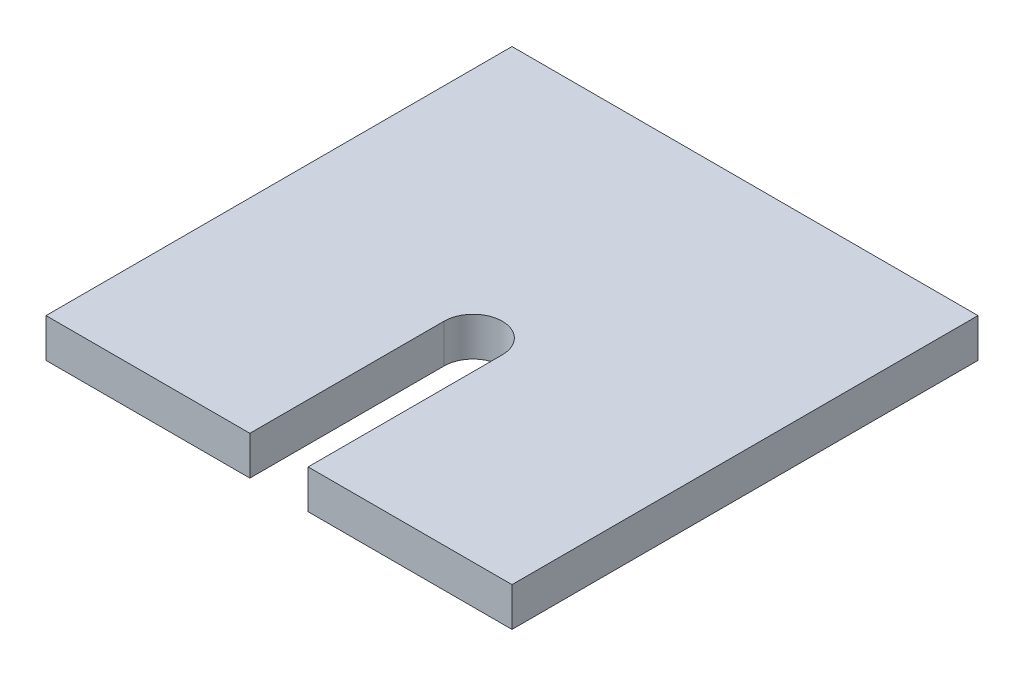
SolidWorks part; units mm, degrees
material "Cedar"
ref_plane "Front Plane" through (0, 0, 0) normal (0, 0, 1) x (1, 0, 0)
ref_plane "Top Plane" through (0, 0, 0) normal (0, 1, 0) x (1, 0, 0)
ref_plane "Right Plane" through (0, 0, 0) normal (1, 0, 0) x (0, 0, -1)
sketch "Sketch9" plane through (0, 0, 0) normal (0, 1, 0) x (1, 0, 0)
  line L0 (-30.3095, -47.7547) -> (3.028, -47.7547)
  line L1 (-73.172, 28.4453) -> (3.028, 28.4453)
  line L2 (-73.172, 28.4453) -> (-73.172, -47.7547)
  line L3 (-73.172, -47.7547) -> (-39.8345, -47.7547)
  line L4 (3.028, 28.4453) -> (3.028, -47.7547)
  line L5 (-35.072, -47.7547) -> (-35.072, 28.4453) construction
  line L6 (-73.172, -9.6547) -> (3.028, -9.6547) construction
  line L8 (-30.3095, -16.0047) -> (-30.3095, -47.7547)
  line L10 (-39.8345, -16.0047) -> (-39.8345, -47.7547)
  line L11 (-30.3095, -16.0047) -> (-39.8345, -47.7547) construction
  line L12 (-30.3095, -47.7547) -> (-39.8345, -16.0047) construction
  arc A0 (-30.3095, -16.0047) -> (-39.8345, -16.0047) centre (-35.072, -16.0047) ccw
  point P4 (-35.072, -31.8797)
  point P108 (-35.072, -9.6547)
  dimension "D3" = 9.525
  dimension "D1" = 76.2
  dimension "D2" = 76.2
  dimension "D4" = 31.75
extrude "Boss-Extrude1" add sketch "Sketch9" along normal blind 6.35 contours L2 L3 L10 A0 L8 L0 L4 L1
